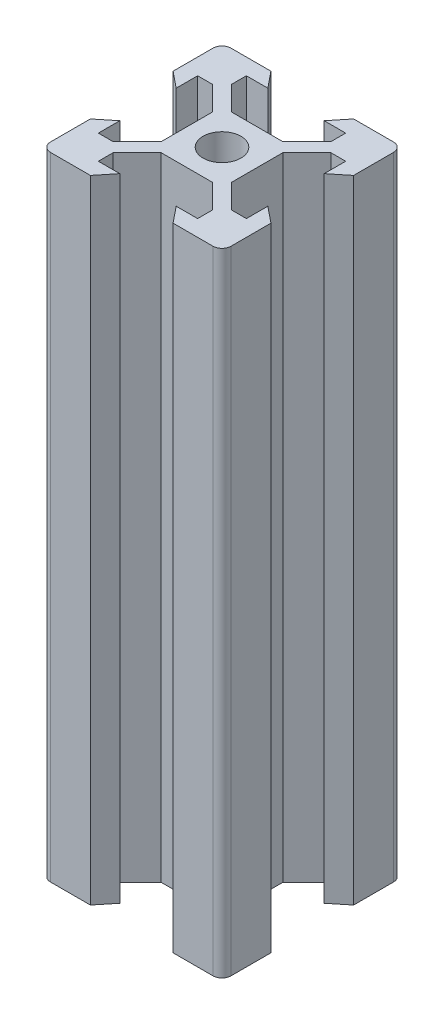
SolidWorks part; units mm, degrees
ref_plane "Front Plane" through (0, 0, 0) normal (0, 0, 1) x (1, 0, 0)
ref_plane "Top Plane" through (0, 0, 0) normal (0, 1, 0) x (1, 0, 0)
ref_plane "Right Plane" through (0, 0, 0) normal (1, 0, 0) x (0, 0, -1)
sketch "Sketch1" plane through (0, 0, 0) normal (0, 1, 0) x (1, 0, 0)
  line L0 (-3.125, 8.2) -> (-4.58, 10)
  line L1 (-9, 10) -> (9, 10)
  line L2 (-10, 9) -> (-10, -9)
  line L3 (-9, -10) -> (9, -10)
  line L4 (10, 9) -> (10, -9)
  line L5 (-10, 10) -> (10, -10) construction
  line L6 (-10, -10) -> (10, 10) construction
  line L7 (-10, 0) -> (0, 0) construction
  line L8 (0, 10) -> (0, 0) construction
  line L9 (-8.2, 3.125) -> (-10, 4.58)
  line L10 (-8.2, 3.125) -> (-8.2, 5.5)
  line L11 (-3.125, 8.2) -> (-5.5, 8.2)
  line L12 (-5.5, 8.2) -> (-5.5, 6.56)
  line L13 (-2.84, 3.9) -> (2.84, 3.9)
  line L14 (-5.5, 6.56) -> (-2.84, 3.9)
  line L15 (-8.2, 5.5) -> (-6.56, 5.5)
  line L16 (-6.56, 5.5) -> (-3.9, 2.84)
  line L17 (-3.9, 2.84) -> (-3.9, -2.84)
  line L18 (3.9, 2.84) -> (3.9, -2.84)
  line L19 (6.56, 5.5) -> (3.9, 2.84)
  line L20 (8.2, 5.5) -> (6.56, 5.5)
  line L21 (8.2, 3.125) -> (8.2, 5.5)
  line L22 (8.2, 3.125) -> (10, 4.58)
  line L23 (3.125, 8.2) -> (4.58, 10)
  line L24 (3.125, 8.2) -> (5.5, 8.2)
  line L25 (5.5, 8.2) -> (5.5, 6.56)
  line L26 (5.5, 6.56) -> (2.84, 3.9)
  line L27 (-8.2, -3.125) -> (-10, -4.58)
  line L28 (-8.2, -3.125) -> (-8.2, -5.5)
  line L29 (-8.2, -5.5) -> (-6.56, -5.5)
  line L30 (-6.56, -5.5) -> (-3.9, -2.84)
  line L31 (8.2, -3.125) -> (10, -4.58)
  line L32 (8.2, -3.125) -> (8.2, -5.5)
  line L33 (8.2, -5.5) -> (6.56, -5.5)
  line L34 (6.56, -5.5) -> (3.9, -2.84)
  line L35 (5.5, -6.56) -> (2.84, -3.9)
  line L36 (5.5, -8.2) -> (5.5, -6.56)
  line L37 (3.125, -8.2) -> (5.5, -8.2)
  line L38 (3.125, -8.2) -> (4.58, -10)
  line L39 (-5.5, -6.56) -> (-2.84, -3.9)
  line L40 (-2.84, -3.9) -> (2.84, -3.9)
  line L41 (-5.5, -8.2) -> (-5.5, -6.56)
  line L42 (-3.125, -8.2) -> (-5.5, -8.2)
  line L43 (-3.125, -8.2) -> (-4.58, -10)
  circle A0 centre (0, 0) radius 2.1
  arc A1 (-10, -9) -> (-9, -10) centre (-9, -9) ccw
  arc A2 (9, -10) -> (10, -9) centre (9, -9) ccw
  arc A3 (9, 10) -> (10, 9) centre (9, 9) cw
  arc A4 (-9, 10) -> (-10, 9) centre (-9, 9) ccw
  point P0 (0, 0)
  point P35 (0, 3.9)
  point P40 (-3.9, 0)
  point P41 (3.9, 0)
  dimension "D3" = 4.2
  dimension "D2" = 1
  dimension "D1" = 20
  dimension "D4" = 6.1
  dimension "D5" = 6.25
  dimension "D6" = 11
  dimension "D7" = 5.68
  dimension "D8" = 9.16
  dimension "D9" = 1.8
extrude "Boss-Extrude1" add sketch "Sketch1" along normal blind 70 contours L43 L42 L41 L39 L40 L35 L36 L37 L38 L3 L4 L31 L32 L33 L34 L18 L19 L20 L21 L22 L1 L23 L24 L25 L26 L13 L14 L12 L11 L0 L2 L9 L10 L15 L16 L17 L30 L29 L28 L27 A0
